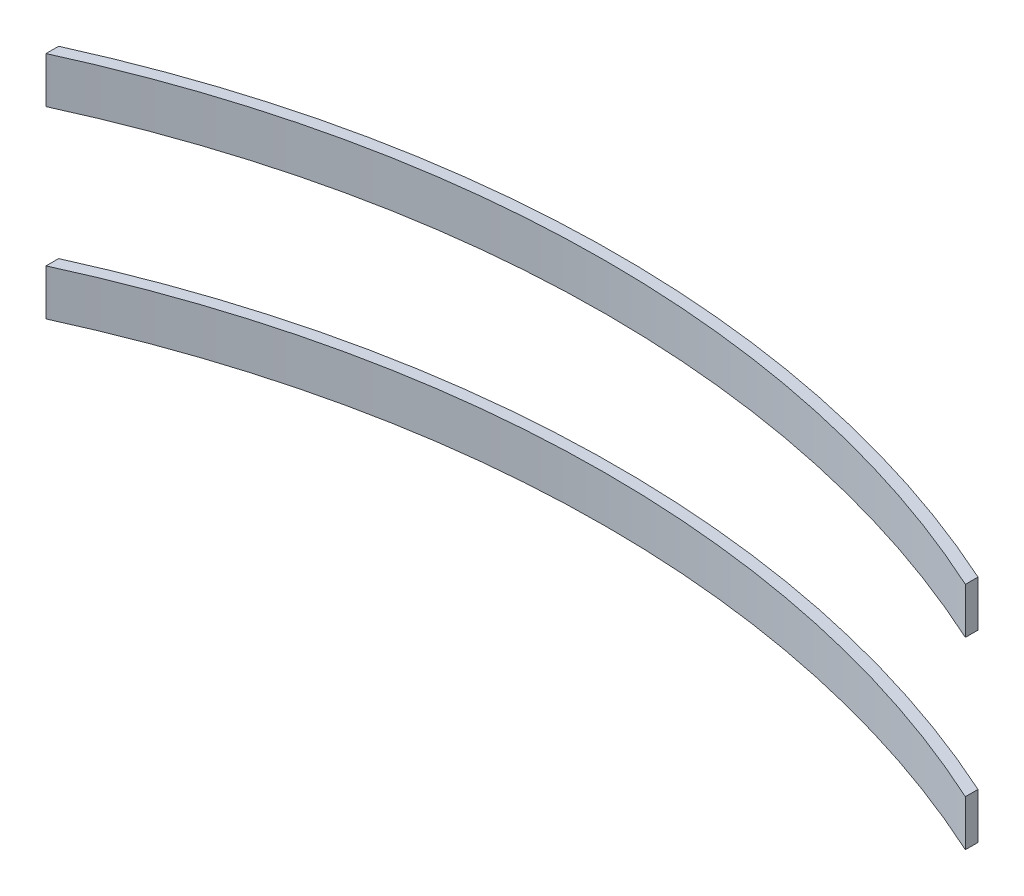
SolidWorks part; units mm, degrees
ref_plane "Front Plane" through (0, 0, 0) normal (0, 0, 1) x (1, 0, 0)
ref_plane "Top Plane" through (0, 0, 0) normal (0, 1, 0) x (1, 0, 0)
ref_plane "Right Plane" through (0, 0, 0) normal (1, 0, 0) x (0, 0, -1)
sketch "Sketch9" plane through (0, 0, 0) normal (0, 1, 0) x (1, 0, 0)
  line L1 (-20, 99.8263) -> (-20, 3.8945) construction
  line L2 (20, 97.6892) -> (20, 3.8945) construction
  line L3 (0, -55) -> (0, 55) construction
  line L4 (-20, 44.1843) -> (-20, 43.6348)
  line L5 (20, 44.1843) -> (20, 43.6348)
  arc A0 (-20, 44.1843) -> (20, 44.1843) centre (0, 0) cw
  arc A1 (20, 43.6348) -> (-20, 43.6348) centre (0, 0) ccw
  dimension "D3" = 48.5
  dimension "D4" = 48
  dimension "D1" = 20
  dimension "D2" = 20
extrude "Boss-Extrude1" add sketch "Sketch9" along normal blind 2 contours A0 L5 A1 L4
ref_plane "Plane6" through (0, 8, 0) normal (0, 1, 0) x (1, 0, 0)
sketch "Sketch11" plane through (0, 8, 0) normal (0, 1, 0) x (1, 0, 0)
  line L1 (20, 44.1843) -> (20, 43.6348)
  line L2 (-20, 44.1843) -> (-20, 43.6348)
  line L3 (0, -1.1) -> (0, 1.1) construction
  arc A0 (20, 43.6348) -> (-20, 43.6348) centre (0, 0) ccw
  arc A1 (20, 44.1843) -> (-20, 44.1843) centre (0, 0) ccw
  dimension "D1" = 96
  dimension "D2" = 97
  dimension "D3" = 20
  dimension "D4" = 20
sketch "Sketch12" plane through (0, 0, 0) normal (0, 1, 0) x (1, 0, 0)
  line L0 (25, 45.1179) -> (25, 5.3758) construction
  line L1 (-25, 46.8777) -> (-25, 4.8626) construction
  line L2 (0, -5.5) -> (0, 5.5) construction
  dimension "D1" = 25
  dimension "D2" = 25
extrude "Boss-Extrude2" add sketch "Sketch11" along normal blind 2 separate body contours A1 L2 A0 L1
